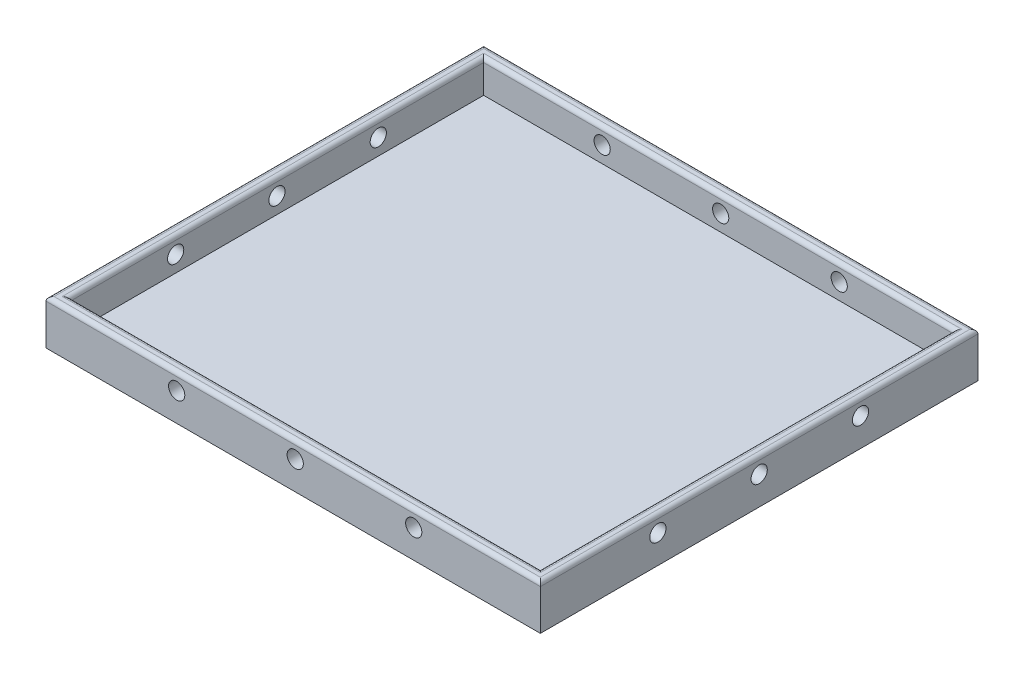
SolidWorks part; units mm, degrees
ref_plane "Front Plane" through (0, 0, 0) normal (0, 0, 1) x (1, 0, 0)
ref_plane "Top Plane" through (0, 0, 0) normal (0, 1, 0) x (1, 0, 0)
ref_plane "Right Plane" through (0, 0, 0) normal (1, 0, 0) x (0, 0, -1)
sketch "Sketch1" plane through (0, 0, 0) normal (0, 1, 0) x (1, 0, 0)
  line L1 (-201.6099, 77.8947) -> (-79.6099, 77.8947)
  line L2 (-201.6099, 77.8947) -> (-201.6099, -30.1053)
  line L3 (-201.6099, -30.1053) -> (-79.6099, -30.1053)
  line L4 (-79.6099, 77.8947) -> (-79.6099, -30.1053)
  dimension "D1" = 122
  dimension "D2" = 108
extrude "Boss-Extrude1" add sketch "Sketch1" along normal blind 11
sketch "Sketch4" plane through (0, 11, 0) normal (0, 1, 0) x (1, 0, 0)
  line L0 (-201.6099, 77.8947) -> (-201.6099, -30.1053) construction
  line L1 (-198.6099, 74.8947) -> (-82.6099, 74.8947)
  line L2 (-198.6099, 74.8947) -> (-198.6099, -27.1053)
  line L3 (-198.6099, -27.1053) -> (-82.6099, -27.1053)
  line L4 (-82.6099, 74.8947) -> (-82.6099, -27.1053)
  line L5 (-79.6099, 77.8947) -> (-201.6099, 77.8947) construction
  line L6 (-79.6099, -30.1053) -> (-79.6099, 77.8947) construction
  line L7 (-201.6099, -30.1053) -> (-79.6099, -30.1053) construction
  dimension "D1" = 3
  dimension "D2" = 3
  dimension "D3" = 3
  dimension "D4" = 3
extrude "Cut-Extrude1" cut sketch "Sketch4" against normal blind 8
sketch "Sketch5" plane through (0, 0, -74.8947) normal (0, 0, 1) x (1, 0, 0)
  line L0 (-198.6099, 3) -> (-198.6099, 11) construction
  line L1 (-82.6099, 3) -> (-198.6099, 3) construction
  circle A0 centre (-169.3599, 7) radius 2
  circle A1 centre (-140.1099, 7) radius 2
  circle A2 centre (-110.8599, 7) radius 2
  dimension "D1" = 29.25
  dimension "D2" = 29.25
  dimension "D3" = 29.25
  dimension "D4" = 4
  dimension "D5" = 4
  dimension "D6" = 4
sketch "Sketch6" plane through (-198.6099, 0, 0) normal (1, 0, 0) x (0, 0, -1)
  line L0 (-27.1053, 3) -> (-27.1053, 11) construction
  line L1 (74.8947, 3) -> (74.8947, 11) construction
  line L2 (74.8947, 3) -> (-27.1053, 3) construction
  circle A0 centre (-1.1053, 7) radius 2
  circle A1 centre (23.8947, 7) radius 2
  circle A2 centre (48.8947, 7) radius 2
  dimension "D1" = 26
  dimension "D2" = 25
  dimension "D3" = 25
  dimension "D4" = 26
  dimension "D5" = 4
extrude "Cut-Extrude6" cut sketch "Sketch6" against normal through all both and the other way through all
extrude "Cut-Extrude5" cut sketch "Sketch5" against normal through all both and the other way through all
fillet "Fillet2" radius 1 8 edges at (-140.6099, 11, 27.1053) (-140.6099, 11, 30.1053) (-79.6099, 11, -23.8947) (-82.6099, 11, -23.8947) (-198.6099, 11, -23.8947) (-140.6099, 11, -74.8947) (-201.6099, 11, -23.8947) (-140.6099, 11, -77.8947)
